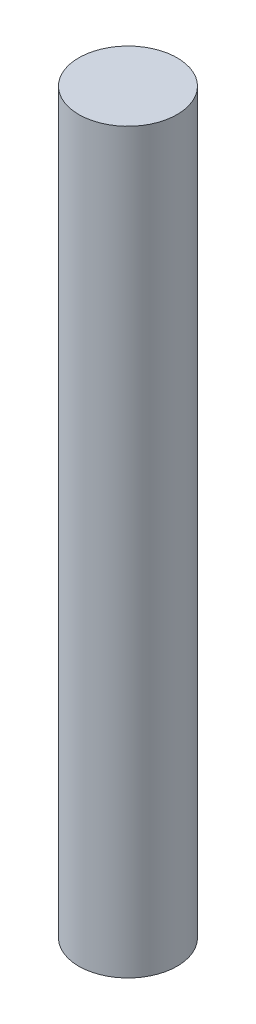
SolidWorks part; units mm, degrees
ref_plane "Front Plane" through (0, 0, 0) normal (0, 0, 1) x (1, 0, 0)
ref_plane "Top Plane" through (0, 0, 0) normal (0, 1, 0) x (1, 0, 0)
ref_plane "Right Plane" through (0, 0, 0) normal (1, 0, 0) x (0, 0, -1)
sketch "Sketch1" plane through (0, 0, 0) normal (0, 1, 0) x (1, 0, 0)
  circle A0 centre (0, 0) radius 9
  dimension "D1" = 18
extrude "Boss-Extrude1" add sketch "Sketch1" along normal blind 135
